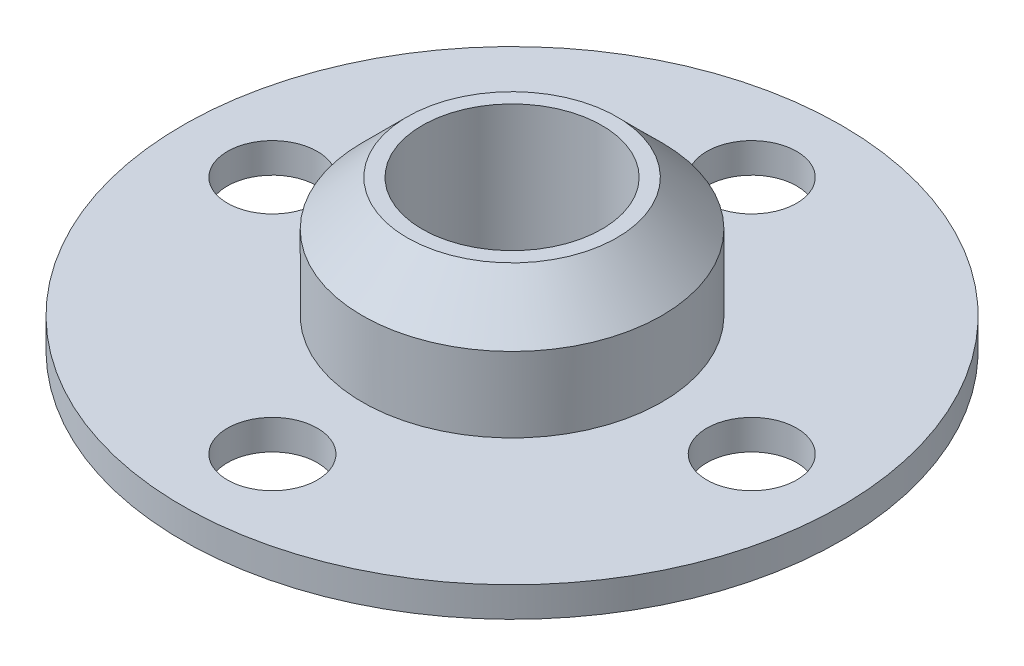
SolidWorks part; units mm, degrees
material "PEI"
ref_plane "Front Plane" through (0, 0, 0) normal (0, 0, 1) x (1, 0, 0)
ref_plane "Top Plane" through (0, 0, 0) normal (0, 1, 0) x (1, 0, 0)
ref_plane "Right Plane" through (0, 0, 0) normal (1, 0, 0) x (0, 0, -1)
sketch "Sketch1" plane through (0, 0, 0) normal (0, 1, 0) x (1, 0, 0)
  circle A0 centre (0, 0) radius 3
  circle A1 centre (0, 0) radius 5
  dimension "D1" = 6
  dimension "12" = 10
extrude "Boss-Extrude1" add sketch "Sketch1" along normal blind 5
chamfer "Chamfer1" distance 1.5 angle 45 1 edges at (0, 5, 5)
sketch "Sketch2" plane through (0, 0, 0) normal (0, -1, 0) x (1, 0, 0)
  line L0 (0, 0) -> (8, 0)
  line L1 (0, 0) -> (0, 8)
  circle A0 centre (0, 0) radius 8
  circle A1 centre (0, 0) radius 5
  circle A2 centre (0, 0) radius 5
  circle A3 centre (8, 0) radius 1.5
  circle A4 centre (0, -8) radius 1.5
  circle A5 centre (-8, 0) radius 1.5
  circle A6 centre (0, 8) radius 1.5
  circle A7 centre (0, 0) radius 11
  circle M2 centre (0, 0) radius 5
  circle M3 centre (0, 0) radius 3
  dimension "D2" = 16
  dimension "D3" = 4
  dimension "3" = 3
  dimension "D5" = 22
  dimension "D4" = 16
  dimension "D1" = 0
extrude "Boss-Extrude2" add sketch "Sketch2" against normal blind 1 contours A7 A6 A0 A3 A4 A5 | A6 A0 A5 A4 A3 L0 L1 M2 | L1 L0 M3 M2 | L1 L0 M3 M2 | A6 L1 L0 A3 A0 M2
